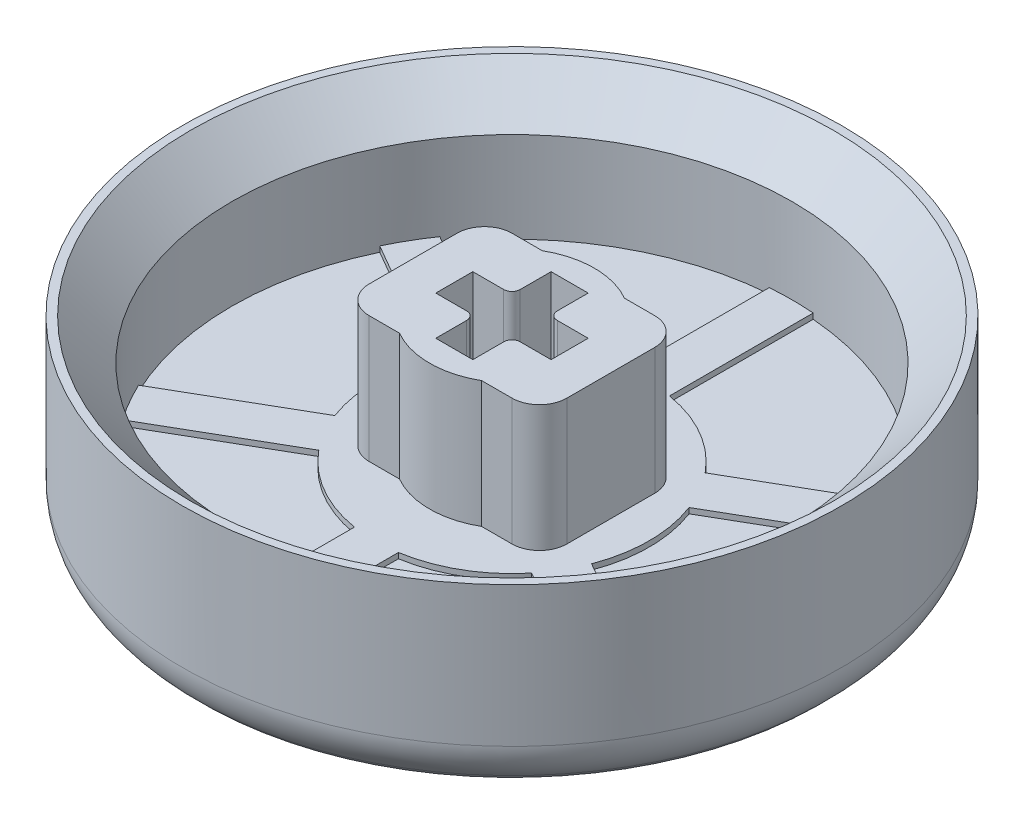
SolidWorks part; units mm, degrees
ref_plane "Front Plane" through (0, 0, 0) normal (0, 0, 1) x (1, 0, 0)
ref_plane "Top Plane" through (0, 0, 0) normal (0, 1, 0) x (1, 0, 0)
ref_plane "Right Plane" through (0, 0, 0) normal (1, 0, 0) x (0, 0, -1)
sketch "Sketch1" plane through (0, 0, 0) normal (0, 1, 0) x (1, 0, 0)
  circle A0 centre (0, 0) radius 12
  dimension "D1" = 24
extrude "button top" add sketch "Sketch1" along normal blind 1.8
sketch "Sketch2" plane through (0, 1.8, 0) normal (0, 1, 0) x (1, 0, 0)
  circle A3 centre (0, 0) radius 12
  circle A4 centre (0, 0) radius 12 construction
  circle A5 centre (0, 0) radius 10.2
  dimension "D1" = 1.8
extrude "button walls" add sketch "Sketch2" along normal blind 4.8
sketch "Sketch5" plane through (0, 1.8, 0) normal (0, 1, 0) x (1, 0, 0)
  circle A0 centre (0, 0) radius 5
  dimension "D1" = 10
extrude "offset" add sketch "Sketch5" along normal blind 0.2
sketch "Sketch3" plane through (0, 1.8, 0) normal (0, 1, 0) x (1, 0, 0)
  line L0 (0, -2.1) -> (0, 2.1) construction
  line L1 (-2.1, 0) -> (2.1, 0) construction
  line L2 (-0.675, 0.975) -> (-0.675, 2.1)
  line L3 (-0.675, -2.1) -> (0.675, -2.1)
  line L4 (-0.675, -2.1) -> (-0.675, -0.975)
  line L5 (-0.675, 2.1) -> (0.675, 2.1)
  line L6 (0.675, -2.1) -> (0.675, -0.975)
  line L7 (-0.675, -2.1) -> (0.675, 2.1) construction
  line L8 (-0.675, 2.1) -> (0.675, -2.1) construction
  line L9 (-2.1, -0.675) -> (-0.975, -0.675)
  line L10 (-2.1, -0.675) -> (-2.1, 0.675)
  line L11 (-2.1, 0.675) -> (-0.975, 0.675)
  line L12 (2.1, -0.675) -> (2.1, 0.675)
  line L13 (-2.1, -0.675) -> (2.1, 0.675) construction
  line L14 (-2.1, 0.675) -> (2.1, -0.675) construction
  line L15 (0.975, 0.675) -> (2.1, 0.675)
  line L16 (0.675, 0.975) -> (0.675, 2.1)
  line L17 (0.975, -0.675) -> (2.1, -0.675)
  line L19 (-3.6, -2.6) -> (3.6, -2.6)
  line L20 (-3.6, -2.6) -> (-3.6, 2.6)
  line L21 (-3.6, 2.6) -> (3.6, 2.6)
  line L22 (3.6, -2.6) -> (3.6, 2.6)
  line L23 (-3.6, -2.6) -> (3.6, 2.6) construction
  line L24 (-3.6, 2.6) -> (3.6, -2.6) construction
  arc A1 (-0.675, -0.975) -> (-0.975, -0.675) centre (-0.975, -0.975) ccw
  arc A2 (0.675, -0.975) -> (0.975, -0.675) centre (0.975, -0.975) cw
  arc A3 (0.975, 0.675) -> (0.675, 0.975) centre (0.975, 0.975) cw
  arc A4 (-0.675, 0.975) -> (-0.975, 0.675) centre (-0.975, 0.975) cw
  circle A5 centre (0, 0) radius 3
  point P0 (0, 0)
  point P6 (0, 0)
  point P9 (0, 0)
  point P22 (2.1, 0)
  point P24 (0, 2.1)
  point P29 (0.675, -0.675)
  point P32 (0.675, 0.675)
  dimension "D1" = 7.2
  dimension "D4" = 0.3
  dimension "D6" = 6
  dimension "D2" = 4.2
  dimension "D3" = 1.35
  dimension "D5" = 5.2
extrude "stem housing" add sketch "Sketch3" along normal blind 4.6 from surface at 0.2 contours A5 L19 L22 L21 | L19 A5 L21 A4 L2 L5 L16 A3 L15 L12 L17 A2 L6 L3 L4 A1 L9 L10 L11 | L19 A5 | A5 L21 L20 L19 | L21 A5 starting at face at (0, 2, 5)
sketch "Sketch4" plane through (0, 1.8, 0) normal (0, 1, 0) x (1, 0, 0)
  line L0 (0, 3.9185) -> (0, 10.2) construction
  line L1 (-0.8, 3.9185) -> (-0.8, 10.2)
  line L2 (0.8, 3.9185) -> (0.8, 10.2)
  line L3 (-3.3935, 1.9593) -> (-8.8335, 5.1) construction
  line L4 (-3.7935, 1.2664) -> (-9.2335, 4.4072)
  line L5 (-2.9935, 2.6521) -> (-8.4335, 5.7928)
  line L6 (-3.3935, -1.9593) -> (-8.8335, -5.1) construction
  line L7 (-2.9935, -2.6521) -> (-8.4335, -5.7928)
  line L8 (-3.7935, -1.2664) -> (-9.2335, -4.4072)
  line L9 (0, -3.9185) -> (0, -10.2) construction
  line L10 (0.8, -3.9185) -> (0.8, -10.2)
  line L11 (-0.8, -3.9185) -> (-0.8, -10.2)
  line L12 (3.3935, -1.9593) -> (8.8335, -5.1) construction
  line L13 (3.7935, -1.2664) -> (9.2335, -4.4072)
  line L14 (2.9935, -2.6521) -> (8.4335, -5.7928)
  line L15 (3.3935, 1.9593) -> (8.8335, 5.1) construction
  line L16 (2.9935, 2.6521) -> (8.4335, 5.7928)
  line L17 (3.7935, 1.2664) -> (9.2335, 4.4072)
  circle A2 centre (0, 0) radius 10.2 construction
  arc A3 (-0.8, 3.9185) -> (0.8, 3.9185) centre (0, 3.9185) ccw
  arc A4 (0.8, 10.2) -> (-0.8, 10.2) centre (0, 10.2) ccw
  arc A5 (-3.7935, 1.2664) -> (-2.9935, 2.6521) centre (-3.3935, 1.9593) ccw
  arc A6 (-8.4335, 5.7928) -> (-9.2335, 4.4072) centre (-8.8335, 5.1) ccw
  arc A7 (-2.9935, -2.6521) -> (-3.7935, -1.2664) centre (-3.3935, -1.9593) ccw
  arc A8 (-9.2335, -4.4072) -> (-8.4335, -5.7928) centre (-8.8335, -5.1) ccw
  arc A9 (0.8, -3.9185) -> (-0.8, -3.9185) centre (0, -3.9185) ccw
  arc A10 (-0.8, -10.2) -> (0.8, -10.2) centre (0, -10.2) ccw
  arc A11 (3.7935, -1.2664) -> (2.9935, -2.6521) centre (3.3935, -1.9593) ccw
  arc A12 (8.4335, -5.7928) -> (9.2335, -4.4072) centre (8.8335, -5.1) ccw
  arc A13 (2.9935, 2.6521) -> (3.7935, 1.2664) centre (3.3935, 1.9593) ccw
  arc A14 (9.2335, 4.4072) -> (8.4335, 5.7928) centre (8.8335, 5.1) ccw
  point P9 (0, 7.0593)
  point P18 (-6.1135, 3.5296)
  point P25 (-6.1135, -3.5296)
  point P32 (0, -7.0593)
  point P39 (6.1135, -3.5296)
  point P46 (6.1135, 3.5296)
  point P51 (0, 0)
  dimension "D1" = 1.6
  dimension "D2" = 6
extrude "spokes" add sketch "Sketch4" along normal up to surface (0.2 mm away) up to face at (0, 2, 0)
fillet "Fillet1" [suppressed] radius 1.5
chamfer "Chamfer1" distance 1.5 angle 45 1 edges at (0, 6.6, 10.2)
fillet "Fillet2" radius 1 4 edges at (-3.6, 4.3, -2.6) (3.6, 4.3, -2.6) (-3.6, 4.3, 2.6) (3.6, 4.3, 2.6)
ref_axis "Axis1" through (0, 0, 0) along (0, 1, 0)
sketch "Sketch6" plane through (0, 0, 0) normal (0, 0, 1) x (1, 0, 0)
  line L0 (-11.2615, 0) -> (-11.4615, 0.2)
  line L1 (-12, 6.6) -> (-12, 0) construction
  line L2 (-12, 0) -> (12, 0) construction
  line L3 (-12, 1.5) -> (-12, 0)
  line L4 (-12, 0) -> (-11.2615, 0)
  arc A0 (-11.4615, 0.2) -> (-12, 1.5) centre (-10.1615, 1.5) cw
  dimension "D1" = 45
  dimension "D2" = 0.2
  dimension "D3" = 1.5
revolve "Cut-Revolve1" cut sketch "Sketch6" angle 360 about axis through (0, 0, 0) along (0, 1, 0)
